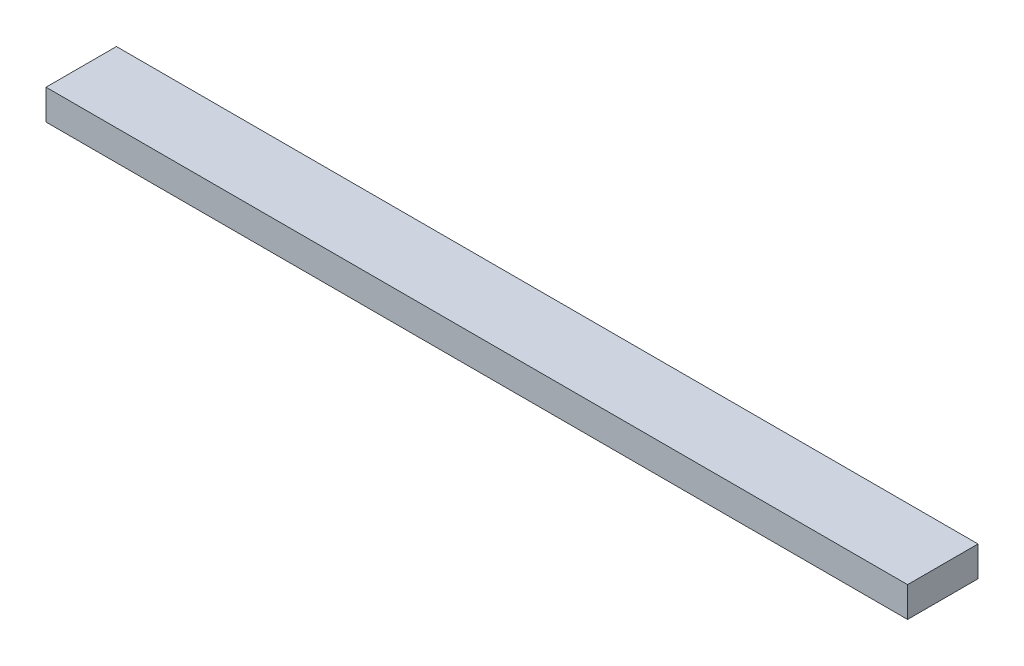
SolidWorks part; units mm, degrees
material "Pine"
ref_plane "Front Plane" through (0, 0, 0) normal (0, 0, 1) x (1, 0, 0)
ref_plane "Top Plane" through (0, 0, 0) normal (0, 1, 0) x (1, 0, 0)
ref_plane "Right Plane" through (0, 0, 0) normal (1, 0, 0) x (0, 0, -1)
sketch "Sketch1" plane through (0, 0, 0) normal (0, 1, 0) x (1, 0, 0)
  line L1 (0, 0) -> (1087.4502, 0)
  line L2 (0, 0) -> (0, 88.9)
  line L3 (0, 88.9) -> (1087.4502, 88.9)
  line L4 (1087.4502, 0) -> (1087.4502, 88.9)
  dimension "D1" = 88.9
  dimension "D2" = 1087.4502
extrude "Boss-Extrude1" add sketch "Sketch1" along normal blind 38.1
